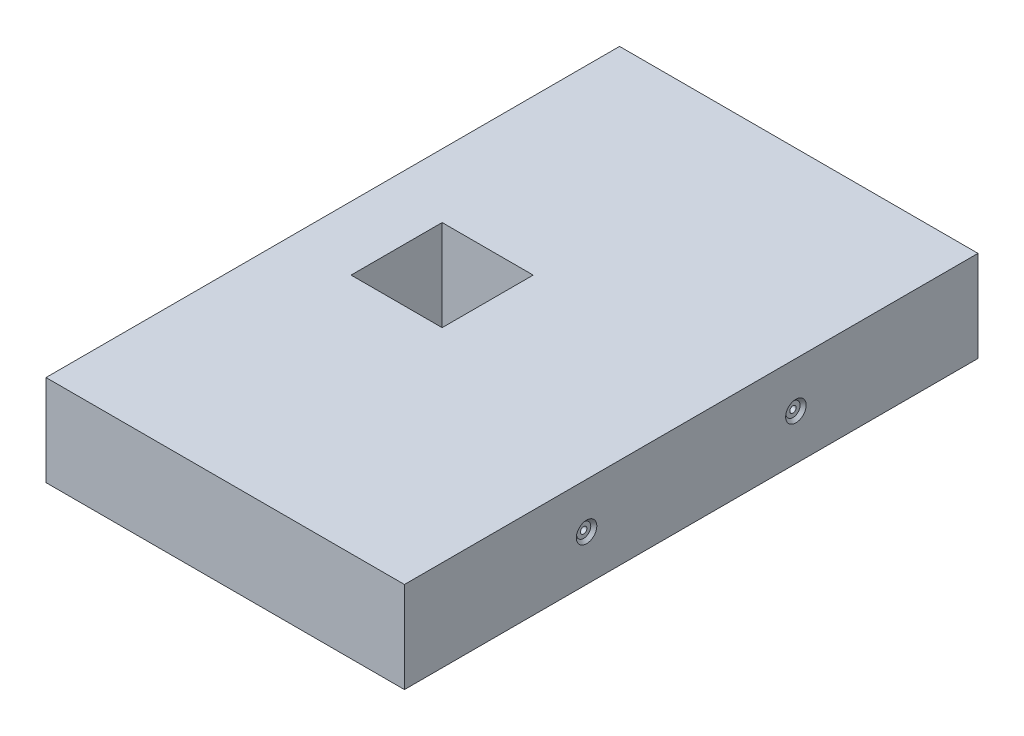
SolidWorks part; units mm, degrees
material "Balsa"
ref_plane "Front Plane" through (0, 0, 0) normal (0, 0, 1) x (1, 0, 0)
ref_plane "Top Plane" through (0, 0, 0) normal (0, 1, 0) x (1, 0, 0)
ref_plane "Right Plane" through (0, 0, 0) normal (1, 0, 0) x (0, 0, -1)
sketch "Sketch1" plane through (0, 0, 0) normal (0, 1, 0) x (1, 0, 0)
  line L1 (-50, 80) -> (50, 80)
  line L2 (-50, 80) -> (-50, -80)
  line L3 (-50, -80) -> (50, -80)
  line L4 (50, 80) -> (50, -80)
  line L5 (-50, 80) -> (50, -80) construction
  line L6 (-50, -80) -> (50, 80) construction
  line L7 (-32.19, 12.7) -> (-6.79, 12.7)
  line L8 (-32.19, 12.7) -> (-32.19, -12.7)
  line L9 (-32.19, -12.7) -> (-6.79, -12.7)
  line L10 (-6.79, 12.7) -> (-6.79, -12.7)
  line L11 (-32.19, 12.7) -> (-6.79, -12.7) construction
  line L12 (-32.19, -12.7) -> (-6.79, 12.7) construction
  point P0 (0, 0)
  point P6 (0, 0)
  dimension "D1" = 100
  dimension "D2" = 160
  dimension "D3" = 25.4
  dimension "D4" = 25.4
  dimension "D5" = 56.79
extrude "Boss-Extrude1" add sketch "Sketch1" along normal blind 25.4
hole_wizard "CBORE for #0 Binding Head Machine Screw1" positions "Sketch2" profile "Sketch3" counterbore size "#0" standard "ANSI Inch"
sketch "Sketch2" plane through (50, 0, 0) normal (1, 0, 0) x (0, 0, -1)
  line L0 (-80, 0) -> (80, 0) construction
  line L2 (80, 25.4) -> (80, 0) construction
  point P0 (-29.2, 12.7)
  point P2 (29.2, 12.7)
  dimension "D1" = 12.7
  dimension "D2" = 58.4
  dimension "D3" = 50.8
sketch "Sketch3" plane through (50, 12.7, 29.2) normal (0, 1, 0) x (0, 0, -1)
  line L0 (0, 0) -> (0, 30.5342)
  line L1 (0, 30.5342) -> (0.889, 30)
  line L2 (0.889, 30) -> (0.889, 0.8128)
  line L3 (0.889, 0.8128) -> (1.985, 0.8128)
  line L5 (1.985, 0.8128) -> (1.985, 0.8725)
  line L6 (1.985, 0.8725) -> (2.8575, 0)
  line L7 (2.8575, 0) -> (0, 0)
  line L8 (-1.985, 0.8725) -> (-2.8575, 0) construction
  line L10 (0, 30.5342) -> (-0.889, 30) construction
  line L11 (0, -6.35) -> (0, 107.95) construction
  dimension "Hole Dia." = 1.778
  dimension "Hole Depth" = 30
  dimension "C'Bore Dia." = 3.97
  dimension "C'Bore Depth" = 0.8128
  dimension "Near C'Sink Dia." = 5.715
  dimension "Near C'Sink Angle" = 90
  dimension "Drill Angle" = 118
